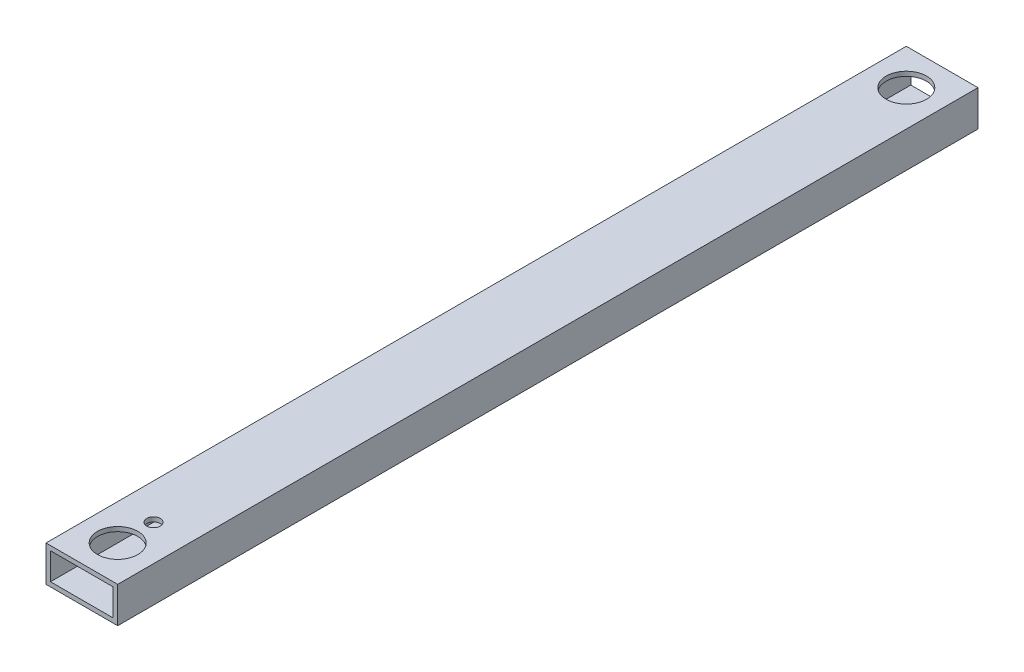
SolidWorks part; units mm, degrees
ref_plane "Front Plane" through (0, 0, 0) normal (0, 0, 1) x (1, 0, 0)
ref_plane "Top Plane" through (0, 0, 0) normal (0, 1, 0) x (1, 0, 0)
ref_plane "Right Plane" through (0, 0, 0) normal (1, 0, 0) x (0, 0, -1)
sketch "Sketch1" plane through (0, 0, 0) normal (0, 0, 1) x (1, 0, 0)
  line L1 (0, 0) -> (50.8, 0)
  line L2 (0, 0) -> (0, 25.4)
  line L3 (0, 25.4) -> (50.8, 25.4)
  line L4 (50.8, 0) -> (50.8, 25.4)
extrude "Boss-Extrude1" add sketch "Sketch1" along normal blind 609.6
sketch "Sketch2" plane through (0, 0, 0) normal (0, 0, -1) x (-1, 0, 0)
  line L1 (-3.175, 3.175) -> (-47.625, 3.175)
  line L2 (-3.175, 3.175) -> (-3.175, 22.225)
  line L3 (-3.175, 22.225) -> (-47.625, 22.225)
  line L4 (-47.625, 3.175) -> (-47.625, 22.225)
extrude "Cut-Extrude1" cut sketch "Sketch2" against normal blind 635
sketch "Sketch6" plane through (0, 25.4, 0) normal (0, 1, 0) x (1, 0, 0)
  line L0 (25.4, 0) -> (25.4, -25.4) construction
  line L1 (50.8, 0) -> (0, 0) construction
  circle A0 centre (25.4, -25.4) radius 14.2875
extrude "Cut-Extrude5" cut sketch "Sketch6" against normal blind 3.175
sketch "Sketch7" plane through (0, 25.4, 0) normal (0, 1, 0) x (1, 0, 0)
  circle A0 centre (25.4, -584.2) radius 14.2875
extrude "Cut-Extrude6" cut sketch "Sketch7" against normal blind 3.175
sketch "Sketch8" plane through (0, 0, 0) normal (0, -1, 0) x (-1, 0, 0)
  line L0 (-25.4, -609.6) -> (-25.4, -558.8) construction
  line L1 (0, -609.6) -> (-50.8, -609.6) construction
  circle A0 centre (-25.4, -558.8) radius 4.7625
extrude "Cut-Extrude7" cut sketch "Sketch8" against normal blind 25.4
